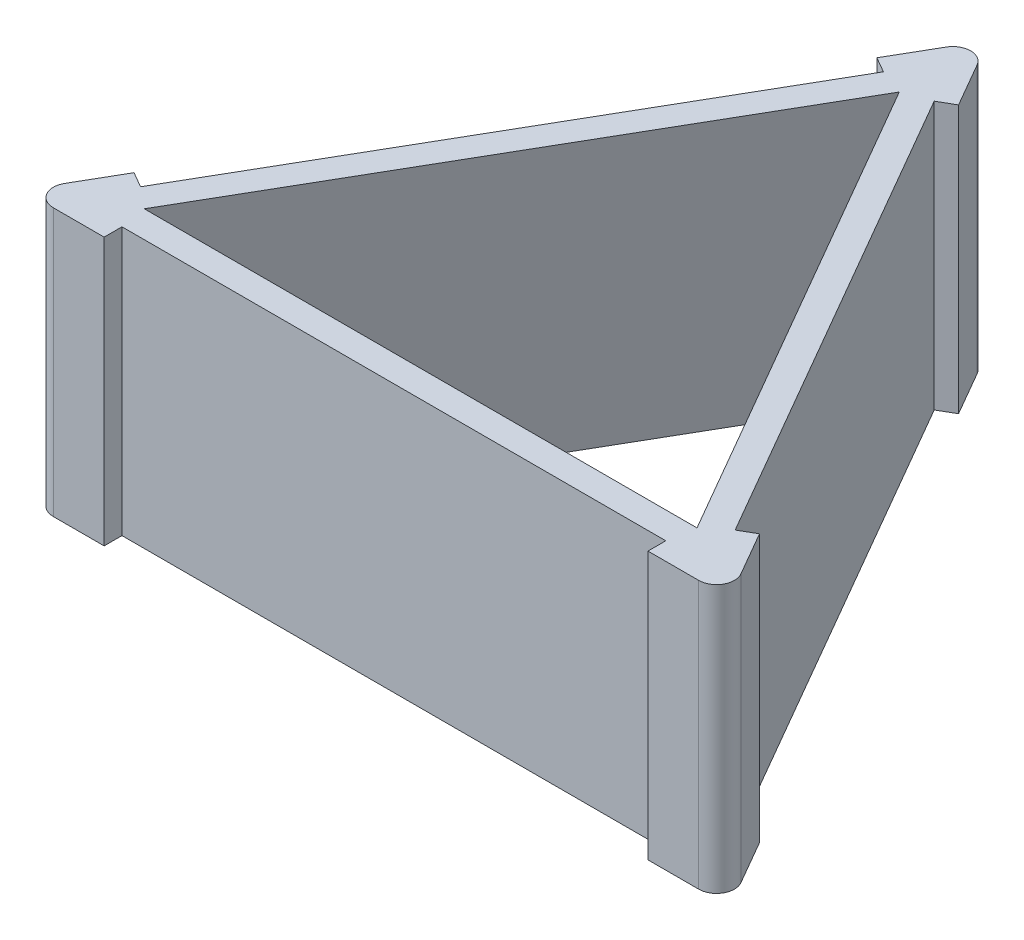
SolidWorks part; units mm, degrees
ref_plane "Front Plane" through (0, 0, 0) normal (0, 0, 1) x (1, 0, 0)
ref_plane "Top Plane" through (0, 0, 0) normal (0, 1, 0) x (1, 0, 0)
ref_plane "Right Plane" through (0, 0, 0) normal (1, 0, 0) x (0, 0, -1)
sketch "Sketch1" plane through (0, 0, 0) normal (0, 1, 0) x (1, 0, 0)
  line L0 (-39.37, -22.7303) -> (39.37, -22.7303)
  line L1 (39.37, -22.7303) -> (0, 45.4606)
  line L2 (0, 45.4606) -> (-39.37, -22.7303)
  line L3 (0, 45.4606) -> (0, -34.7681) construction
  line L4 (39.37, -22.7303) -> (-42.2111, 24.3706) construction
  line L5 (0, 58.1606) -> (-50.3685, -29.0803)
  line L6 (-50.3685, -29.0803) -> (50.3685, -29.0803)
  line L7 (50.3685, -29.0803) -> (0, 58.1606)
  dimension "D1" = 78.74
  dimension "D2" = 6.35
extrude "Boss-Extrude1" add sketch "Sketch1" along normal mid plane 38.1
sketch "Sketch3" plane through (0, 0, 29.0803) normal (0, 0, 1) x (1, 0, 0)
  line L1 (-38.735, 19.05) -> (38.735, 19.05)
  line L2 (-38.735, 19.05) -> (-38.735, -19.05)
  line L3 (-38.735, -19.05) -> (38.735, -19.05)
  line L4 (38.735, 19.05) -> (38.735, -19.05)
  line L5 (-38.735, 19.05) -> (38.735, -19.05) construction
  line L6 (-38.735, -19.05) -> (38.735, 19.05) construction
  point P0 (0, 0)
  dimension "D1" = 38.1
  dimension "D2" = 77.47
extrude "Cut-Extrude1" cut sketch "Sketch3" against normal blind 2.54
sketch "Sketch4" plane through (0, 0, 0) normal (0, 0, 1) x (1, 0, 0)
  line L0 (0, -49.0153) -> (0, 49.7437) construction
pattern_circular "CirPattern1" count 3 over 360 about axis through (0, 0, 0) along (0, 1, 0) of "Cut-Extrude1"
sketch "Sketch6" plane through (0, 19.05, 0) normal (0, 1, 0) x (1, 0, 0)
  line L0 (-50.3685, -29.0803) -> (-44.5518, -19.0054)
  line L1 (-44.5518, -19.0054) -> (-42.3521, -20.2754)
  line L2 (-42.3521, -20.2754) -> (-39.37, -22.7303)
  line L3 (-39.37, -22.7303) -> (-38.735, -26.5403)
  line L4 (-38.735, -26.5403) -> (-38.735, -29.0803)
  line L5 (-38.735, -29.0803) -> (-50.3685, -29.0803)
extrude "Boss-Extrude3" [suppressed] add sketch "Sketch6" along normal blind 5.08
sketch "Sketch8" [suppressed] plane through (0, 0, 29.0803) normal (0, 0, 1) x (1, 0, 0)
  line L0 (-38.735, 19.05) -> (-50.3685, 19.05) construction
  line L1 (-50.3685, 24.13) -> (-50.3685, -19.05) construction
  line L2 (-50.3685, 19.05) -> (-38.735, 24.13) construction
  line L3 (-50.3685, 24.13) -> (-38.735, 19.05) construction
  circle A0 centre (-44.5518, 21.59) radius 1.905
  dimension "D1" = 3.81
mirror "Mirror1" [suppressed] about plane through (0, 0, 0) normal (1, 0, 0)
sketch "Sketch7" [suppressed] plane through (0, 19.05, 0) normal (0, 1, 0) x (1, 0, 0)
  line L0 (-3.6171, 46.8156) -> (-5.8168, 48.0856)
  line L1 (-5.8168, 48.0856) -> (-50.3685, 48.0856)
  line L2 (-50.3685, 48.0856) -> (-44.5518, 58.1606)
  line L3 (-44.5518, 58.1606) -> (44.5518, 58.1606)
  line L4 (44.5518, 58.1606) -> (50.3685, 48.0856)
  line L5 (50.3685, 48.0856) -> (5.8168, 48.0856)
  line L6 (5.8168, 48.0856) -> (3.6171, 46.8156)
  line L7 (3.6171, 46.8156) -> (0, 45.4606)
  line L8 (0, 45.4606) -> (-3.6171, 46.8156)
  point P4 (0, 58.1606)
extrude "Boss-Extrude4" [suppressed] add sketch "Sketch7" along normal blind 5.08
fillet "Fillet1" radius 2.54 3 edges at (0, 0, -58.1606) (50.3685, 0, 29.0803) (-50.3685, 0, 29.0803)
extrude "Cut-Extrude2" [suppressed] cut sketch "Sketch8" against normal up to surface (87.2408 mm away)
mirror "Mirror2" [suppressed] about plane through (0, 0, 0) normal (1, 0, 0)
